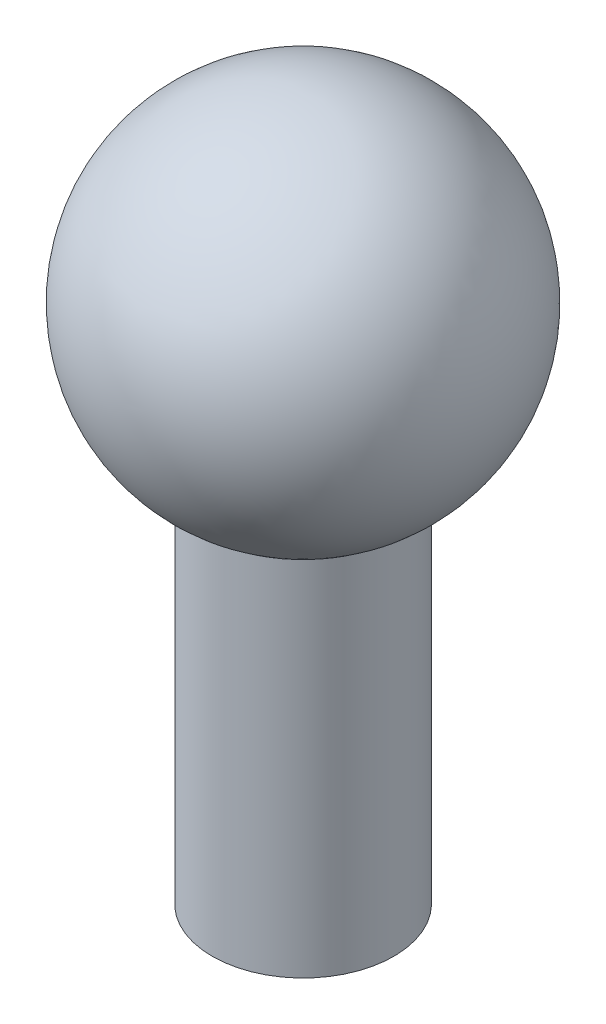
SolidWorks part; units mm, degrees
ref_plane "Plan de face" through (0, 0, 0) normal (0, 0, 1) x (1, 0, 0)
ref_plane "Plan de dessus" through (0, 0, 0) normal (0, 1, 0) x (1, 0, 0)
ref_plane "Plan de droite" through (0, 0, 0) normal (1, 0, 0) x (0, 0, -1)
sketch "Esquisse2" plane through (0, 0, 0) normal (0, 1, 0) x (1, 0, 0)
  circle A0 centre (0, 0) radius 10
  dimension "D1" = 20
extrude "Boss.-Extru.2" add sketch "Esquisse2" along normal blind 40
sketch "Esquisse3" plane through (0, 0, 0) normal (0, -1, 0) x (1, 0, 0)
  circle A0 centre (0, 0) radius 7.25
  dimension "D1" = 14.5
extrude "Enlèv. mat.-Extru.1" cut sketch "Esquisse3" against normal blind 30
cosmetic thread "Représentation de filetage1" parameters "D2"=16
cosmetic thread "Représentation de filetage2" parameters "D2"=16
cosmetic thread "Représentation de filetage3" parameters "D2"=16
cosmetic thread "Représentation de filetage4" parameters "D2"=16
fillet "Congé2" radius 2 1 edges at (0, 30, -7.25)
sketch "Esquisse9" plane through (0, 0, 0) normal (1, 0, 0) x (0, 0, -1)
  line L0 (0, -1000) -> (0, 49000) construction
  line L1 (20, 57.3268) -> (-20, 57.3268)
  arc A1 (20, 57.3268) -> (-20, 57.3268) centre (0, 57.3268) cw
  dimension "D1" = 20
revolve "Révolution7" add sketch "Esquisse9" angle 360 about L1
